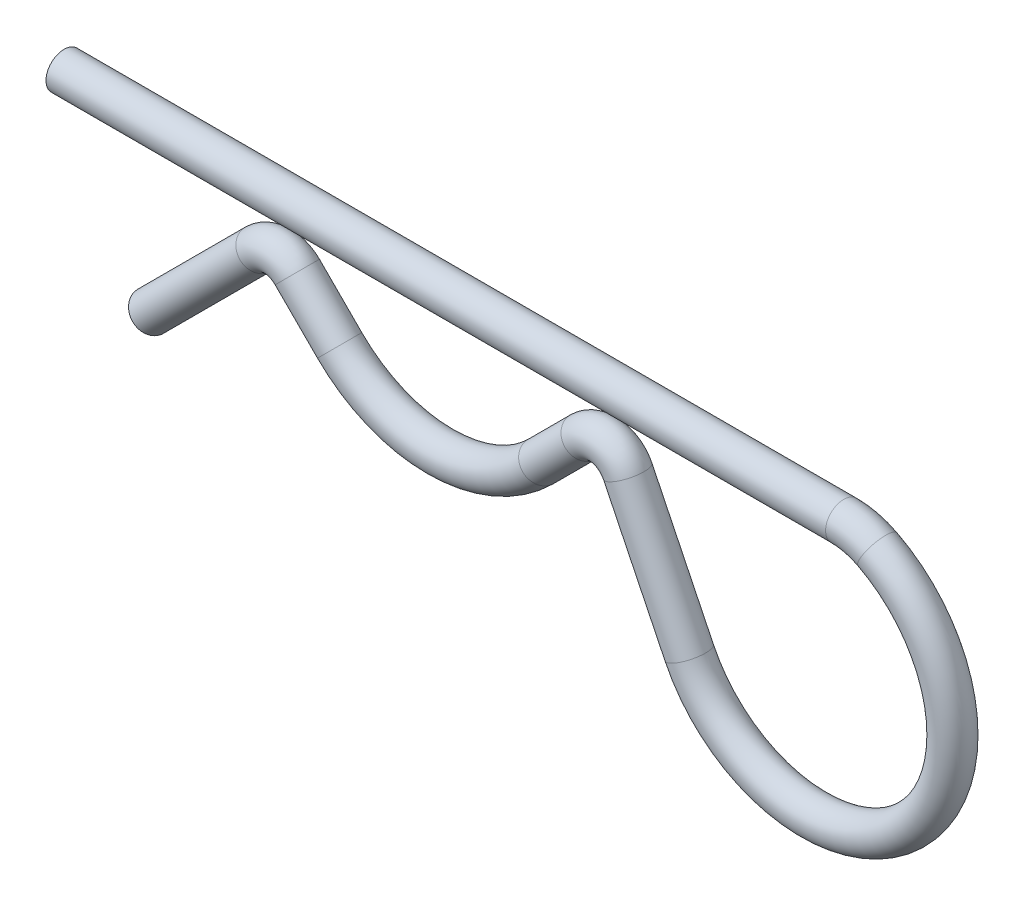
SolidWorks part; units mm, degrees
ref_plane "Face" through (0, 0, 0) normal (0, 0, 1) x (1, 0, 0)
ref_plane "Dessus" through (0, 0, 0) normal (0, 1, 0) x (1, 0, 0)
ref_plane "Droite" through (0, 0, 0) normal (1, 0, 0) x (0, 0, -1)
sketch "Esquisse1" plane through (0, 0, 0) normal (0, 0, 1) x (1, 0, 0)
  line L0 (-26, -0.0798) -> (27.889, -0.0798)
  line L1 (-20.0696, -11.3838) -> (-12.6514, -3.9656)
  line L2 (17.2853, -13.237) -> (13.0356, -4.5046)
  line L3 (6.8943, -6.8943) -> (9.823, -3.9656)
  line L4 (-6.8943, -6.8943) -> (-9.823, -3.9656)
  arc A0 (17.2853, -13.237) -> (30.1796, -0.6353) centre (25.8275, -9.0798) ccw
  arc A1 (-6.8943, -6.8943) -> (6.8943, -6.8943) centre (0, 0) ccw
  arc A2 (-9.823, -3.9656) -> (-12.6514, -3.9656) centre (-11.2372, -5.3798) ccw
  arc A3 (13.0356, -4.5046) -> (9.823, -3.9656) centre (11.2372, -5.3798) ccw
  arc A4 (30.1796, -0.6353) -> (27.889, -0.0798) centre (27.889, -5.0798) ccw
  dimension "D3" = 19
  dimension "D4" = 9
  dimension "D7" = 19.5
  dimension "D8" = 2
  dimension "D5" = 5
  dimension "D1" = 45
  dimension "D2" = 45
  dimension "D6" = 45
  dimension "D9" = 5.3
  dimension "D10" = 5.3
ref_plane "Plan1" through (-26, -0.0798, 0) normal (-1, 0, 0) x (0, 0, 1)
sketch "Esquisse2" plane through (-26, -0.0798, 0) normal (-1, 0, 0) x (0, 0, 1)
  circle A0 centre (0, 0.0798) radius 1.25
  dimension "D1" = 2.5
sweep "Balayage1" add profiles "Esquisse2" path "Esquisse1"
